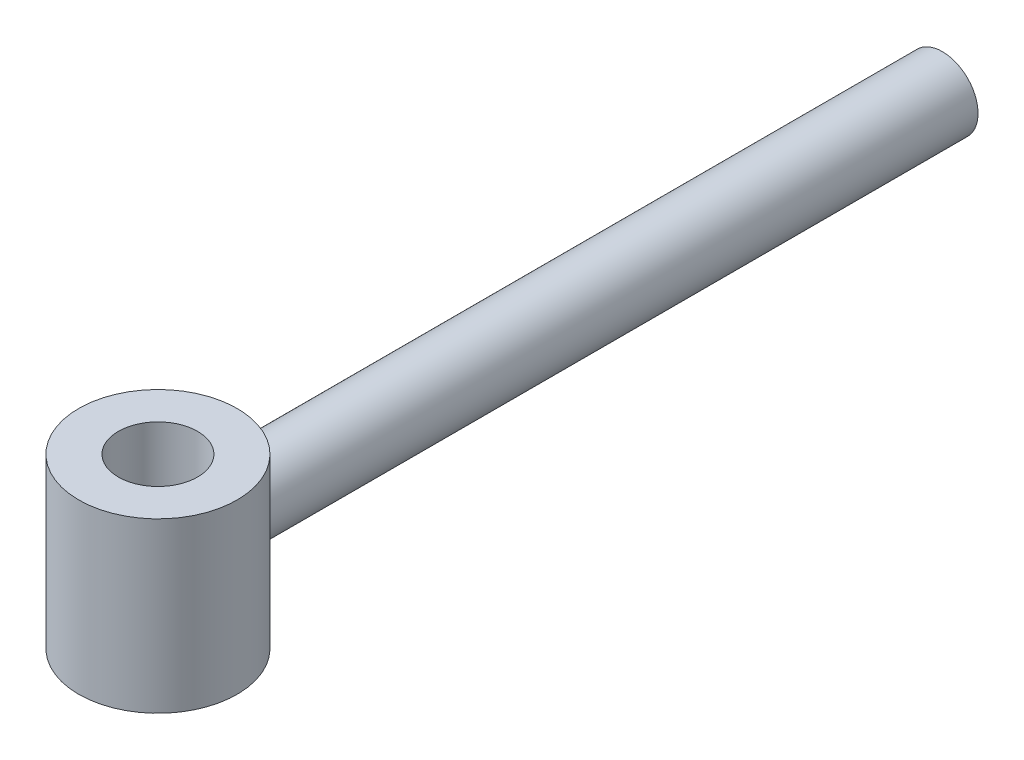
SolidWorks part; units mm, degrees
ref_plane "Front Plane" through (0, 0, 0) normal (0, 0, 1) x (1, 0, 0)
ref_plane "Top Plane" through (0, 0, 0) normal (0, 1, 0) x (1, 0, 0)
ref_plane "Right Plane" through (0, 0, 0) normal (1, 0, 0) x (0, 0, -1)
sketch "Sketch1" plane through (0, 0, 0) normal (0, 1, 0) x (1, 0, 0)
  circle A0 centre (0, 0) radius 20
  circle A1 centre (0, 0) radius 40
  dimension "D2" = 40
  dimension "D1" = 20
extrude "Boss-Extrude1" add sketch "Sketch1" along normal blind 80 and the other way blind 5
ref_plane "Plane1" through (0, 0, -40) normal (0, 0, -1) x (-1, 0, 0)
sketch "Sketch2" plane through (0, 0, -40) normal (0, 0, -1) x (-1, 0, 0)
  line L0 (0, 0) -> (0, 80) construction
  line L1 (20, 80) -> (-20, 80) construction
  circle A1 centre (0, 40) radius 18
  dimension "D1" = 36
extrude "Boss-Extrude2" add sketch "Sketch2" along normal blind 356 and the other way blind 13 separate body
